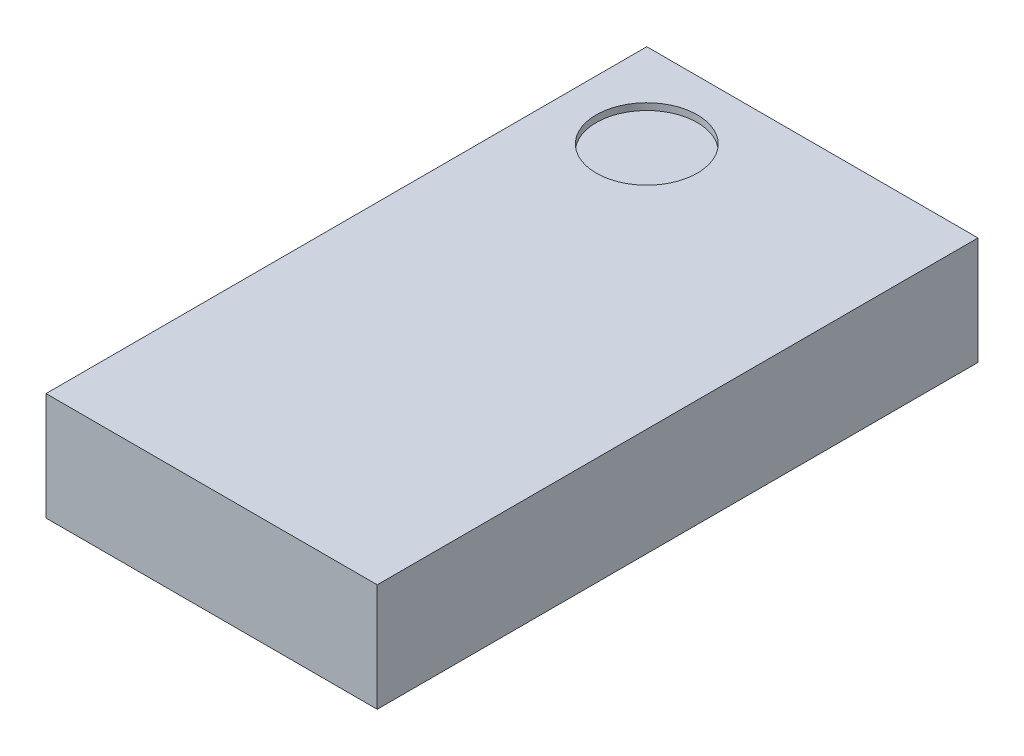
SolidWorks part; units mm, degrees
ref_plane "Front Plane" through (0, 0, 0) normal (0, 0, 1) x (1, 0, 0)
ref_plane "Top Plane" through (0, 0, 0) normal (0, 1, 0) x (1, 0, 0)
ref_plane "Right Plane" through (0, 0, 0) normal (1, 0, 0) x (0, 0, -1)
sketch "Sketch1" plane through (0, 0, 0) normal (0, 1, 0) x (1, 0, 0)
  line L1 (-0.4915, 0.8915) -> (0.4915, 0.8915)
  line L2 (-0.4915, 0.8915) -> (-0.4915, -0.8915)
  line L3 (-0.4915, -0.8915) -> (0.4915, -0.8915)
  line L4 (0.4915, 0.8915) -> (0.4915, -0.8915)
  line L5 (-0.4915, 0.8915) -> (0.4915, -0.8915) construction
  line L6 (-0.4915, -0.8915) -> (0.4915, 0.8915) construction
  point P0 (0, 0)
  dimension "D1" = 1.783
  dimension "D2" = 0.983
extrude "Boss-Extrude1" add sketch "Sketch1" along normal blind 0.32
ref_plane "Plane1" through (0, 0, 0.6) normal (0, 0, 1) x (1, 0, 0)
sketch "Sketch2" plane through (0, 0, 0.6) normal (0, 0, 1) x (1, 0, 0)
  line L0 (-0.4915, 0) -> (0.4915, 0) construction
  line L1 (-0.4915, 0.32) -> (0.4915, 0.32) construction
  line L2 (0, 0) -> (0, -0.2572) construction
  line L3 (-0.2, -0.18) -> (-0.2, 0) construction
  line L4 (-0.3039, 0) -> (-0.2, 0)
  line L5 (-0.2, -0.18) -> (-0.2, 0)
  arc A0 (-0.3039, 0) -> (-0.2, -0.18) centre (-0.2, -0.06) ccw
  arc A1 (-0.2, -0.18) -> (-0.0961, 0) centre (-0.2, -0.06) ccw construction
  point P3 (-0.2, -0.18)
  dimension "D3" = 0.12
  dimension "D1" = 0.5
  dimension "D2" = 0.2
revolve "Revolve1" add sketch "Sketch2" angle 360 about L5
pattern_linear "LPattern1" count 4 spacing 0.4 along (0, 0, -1) count 2 spacing 0.4 along (1, 0, 0) of "Revolve1"
sketch "Sketch3" plane through (0, 0.32, 0) normal (0, 1, 0) x (1, 0, 0)
  line L0 (0.4915, 0.8915) -> (-0.4915, 0.8915) construction
  line L1 (-0.4915, 0.8915) -> (-0.4915, -0.8915) construction
  circle A0 centre (-0.2415, 0.6415) radius 0.15
  dimension "D3" = 0.3
  dimension "D1" = 0.25
  dimension "D2" = 0.25
extrude "Cut-Extrude1" cut sketch "Sketch3" against normal blind 0.02
